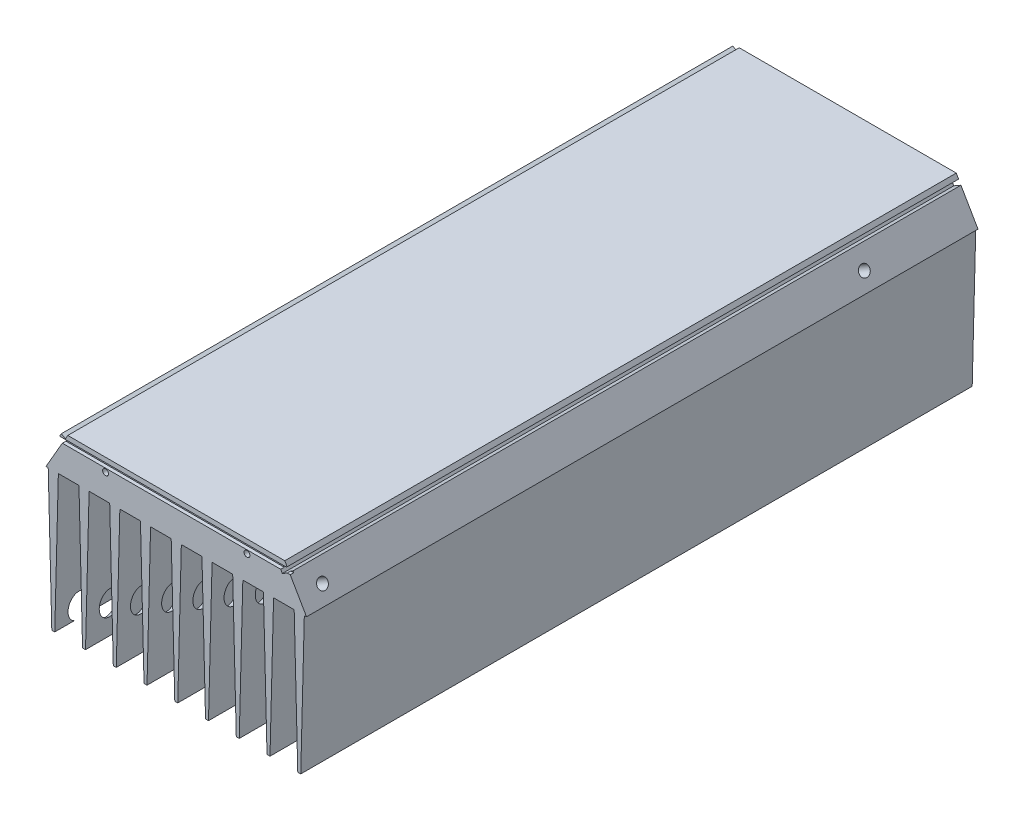
SolidWorks part; units mm, degrees
ref_plane "Plano frontal" through (0, 0, 0) normal (0, 0, 1) x (1, 0, 0)
ref_plane "Plano superior" through (0, 0, 0) normal (0, 1, 0) x (1, 0, 0)
ref_plane "Plano direito" through (0, 0, 0) normal (1, 0, 0) x (0, 0, -1)
sketch "Esboço1" plane through (0, 0, 0) normal (0, 0, 1) x (1, 0, 0)
  line L0 (0, 75) -> (135.77, 75)
  line L1 (135.77, 75) -> (135.77, 0)
  line L2 (0, 75) -> (0, 0)
  line L3 (0, 0) -> (135.77, 0) construction
  line L4 (0, 59) -> (4.785, 59) construction
  line L46 (4.785, 59) -> (13.535, 59)
  line L47 (13.535, 59) -> (17.835, 59) construction
  line L48 (17.835, 59) -> (26.585, 59)
  line L49 (26.585, 59) -> (30.885, 59) construction
  line L50 (30.885, 59) -> (39.635, 59)
  line L51 (39.635, 59) -> (43.935, 59) construction
  line L52 (43.935, 59) -> (52.685, 59)
  line L53 (52.685, 59) -> (56.985, 59) construction
  line L54 (56.985, 59) -> (65.735, 59)
  line L55 (65.735, 59) -> (70.035, 59) construction
  line L56 (70.035, 59) -> (78.785, 59)
  line L57 (78.785, 59) -> (83.085, 59) construction
  line L58 (83.085, 59) -> (91.835, 59)
  line L59 (91.835, 59) -> (96.135, 59) construction
  line L60 (96.135, 59) -> (104.885, 59)
  line L61 (104.885, 59) -> (109.185, 59) construction
  line L62 (109.185, 59) -> (117.935, 59)
  line L63 (117.935, 59) -> (122.235, 59) construction
  line L64 (122.235, 59) -> (130.985, 59)
  line L65 (130.985, 59) -> (135.77, 59) construction
  line L66 (4.785, 59) -> (3.2658, 0)
  line L67 (3.2658, 0) -> (0, 0)
  line L68 (13.535, 59) -> (15.0542, 0)
  line L69 (15.0542, 0) -> (16.3158, 0)
  line L70 (16.3158, 0) -> (17.835, 59)
  line L71 (26.585, 59) -> (28.1042, 0)
  line L72 (28.1042, 0) -> (29.3658, 0)
  line L73 (29.3658, 0) -> (30.885, 59)
  line L74 (39.635, 59) -> (41.1542, 0)
  line L75 (41.1542, 0) -> (42.4158, 0)
  line L76 (42.4158, 0) -> (43.935, 59)
  line L77 (52.685, 59) -> (54.2042, 0)
  line L78 (54.2042, 0) -> (55.4658, 0)
  line L79 (55.4658, 0) -> (56.985, 59)
  line L80 (65.735, 59) -> (67.2542, 0)
  line L81 (67.2542, 0) -> (68.5158, 0)
  line L82 (68.5158, 0) -> (70.035, 59)
  line L83 (78.785, 59) -> (80.3042, 0)
  line L84 (80.3042, 0) -> (81.5658, 0)
  line L85 (81.5658, 0) -> (83.085, 59)
  line L86 (91.835, 59) -> (93.3542, 0)
  line L87 (93.3542, 0) -> (94.6158, 0)
  line L88 (94.6158, 0) -> (96.135, 59)
  line L89 (104.885, 59) -> (106.4042, 0)
  line L90 (106.4042, 0) -> (107.6658, 0)
  line L91 (107.6658, 0) -> (109.185, 59)
  line L92 (117.935, 59) -> (119.4542, 0)
  line L93 (119.4542, 0) -> (120.7158, 0)
  line L94 (120.7158, 0) -> (122.235, 59)
  line L95 (130.985, 59) -> (132.5042, 0)
  line L96 (132.5042, 0) -> (135.77, 0)
  line L97 (67.885, 59) -> (67.885, 75) construction
  line L98 (15.685, 0) -> (15.685, 59) construction
  dimension "D1" = 135.77
  dimension "D2" = 75
  dimension "D3" = 8.75
  dimension "D4" = 4.3
  dimension "D5" = 16
  dimension "D6" = 2.95
extrude "Ressalto-extrusão1" add sketch "Esboço1" along normal blind 285
sketch "Esboço2" plane through (0, 0, 0) normal (0, 0, -1) x (-1, 0, 0)
  line L0 (-21.8312, 75) -> (-20.8312, 73.2679)
  line L1 (-135.77, 75) -> (0, 75) construction
  line L3 (-20.8312, 73.2679) -> (-19.0991, 74.2679)
  line L4 (-19.0991, 74.2679) -> (-18.0991, 72.5359)
  line L5 (-18.0991, 72.5359) -> (-19.8312, 71.5359)
  line L6 (-19.8312, 71.5359) -> (-12.5935, 59)
  line L7 (-4.785, 59) -> (-13.535, 59) construction
  line L8 (-12.5935, 59) -> (-12.5935, -2.8745)
  line L9 (-12.5935, -2.8745) -> (9.5022, -2.8745)
  line L10 (9.5022, -2.8745) -> (9.5022, 75)
  line L11 (9.5022, 75) -> (-21.8312, 75)
  line L12 (-113.9388, 75) -> (-114.9388, 73.2679)
  line L14 (-114.9388, 73.2679) -> (-111.9078, 71.5179)
  line L15 (-111.9078, 71.5179) -> (-112.9078, 69.7859)
  line L16 (-112.9078, 69.7859) -> (-115.9388, 71.5359)
  line L17 (-115.9388, 71.5359) -> (-123.1765, 59)
  line L18 (-122.235, 59) -> (-130.985, 59) construction
  line L19 (-123.1765, 59) -> (-123.1765, -2.8745)
  line L20 (-123.1765, -2.8745) -> (-142.2073, -2.8745)
  line L21 (-142.2073, -2.8745) -> (-142.2073, 78.515)
  line L22 (-142.2073, 78.515) -> (-113.9388, 78.515)
  line L23 (-113.9388, 78.515) -> (-113.9388, 75)
  line L25 (-113.9388, 75) -> (-21.8312, 75) construction
  line L26 (-67.885, 0) -> (-67.885, 75) construction
  line L27 (-67.2542, 0) -> (-68.5158, 0) construction
  dimension "D1" = 60
  dimension "D2" = 2
  dimension "D3" = 2
  dimension "D4" = 3.5
  dimension "D5" = 2
  dimension "D6" = 2
  dimension "D7" = 2
  dimension "D8" = 60
  dimension "D9" = 92.1077
extrude "Corte-extrusão1" cut sketch "Esboço2" against normal through all both and the other way through all
sketch "Esboço3" plane through (117.9301, 68.087, 0) normal (0.866, 0.5, 0) x (0, 0, -1)
  line L0 (-45, -4.0175) -> (-275, -4.0175) construction
  line L2 (-285, 3.9825) -> (0, 3.9825) construction
  line L3 (-285, -10.4927) -> (-285, 3.9825) construction
  circle A0 centre (-275, -4.0175) radius 2.25
  circle A1 centre (-45, -4.0175) radius 2.25
  dimension "D2" = 8
  dimension "D3" = 10
  dimension "D4" = 4.5
  dimension "D1" = 230
extrude "Corte-extrusão2" cut sketch "Esboço3" against normal blind 130
sketch "Esboço4" plane through (-16.1026, 9.2968, 0) normal (-0.866, 0.5, 0) x (0, 0, 1)
  line L0 (275, 63.8675) -> (45, 63.8675) construction
  line L1 (285, 71.8675) -> (285, 57.3923) construction
  line L2 (285, 71.8675) -> (0, 71.8675) construction
  circle A0 centre (45, 63.8675) radius 1.6455
  circle A1 centre (275, 63.8675) radius 1.6455
  dimension "D2" = 10
  dimension "D3" = 8
  dimension "D4" = 3.291
  dimension "D1" = 230
extrude "Corte-extrusão3" cut sketch "Esboço4" against normal blind 15
sketch "Esboço5" plane through (0, 0, 0) normal (0, 0, -1) x (-1, 0, 0)
  line L0 (-113.9388, 75) -> (-21.8312, 75) construction
  line L1 (-67.885, 75) -> (-67.885, 0) construction
  line L2 (-67.2542, 0) -> (-68.5158, 0) construction
  circle A0 centre (-67.885, 49.7676) radius 3.5
  dimension "D1" = 7
  dimension "D2" = 25.2324
extrude "Corte-extrusão4" cut sketch "Esboço5" against normal blind 10
sketch "Esboço6" plane through (117.9301, 68.087, 0) normal (0.866, 0.5, 0) x (0, 0, -1)
  circle A0 centre (-275, -4.0175) radius 4.5
  circle A1 centre (-45, -4.0175) radius 4.5
  dimension "D1" = 9
extrude "Corte-extrusão5" cut sketch "Esboço6" against normal blind 120 from offset 10 offset against normal yes
sketch "Esboço7" plane through (0, 36.4877, 0) normal (1, 0, 0) x (0, 0, -1)
  line L0 (-283.5, 36.5123) -> (-285, 36.5123)
  line L3 (-285, 36.5123) -> (-285, 34.5123)
  line L4 (-285, 34.5123) -> (-283.5, 34.5123)
  line L5 (-283.5, 34.5123) -> (-283.5, 36.5123)
  line L6 (-285, 35.0482) -> (-285, 22.5123) construction
  line L7 (-285, 34.5123) -> (-283.5, 34.5123) construction
  point P3 (-283.5, 36.5123)
  point P4 (-283.5, 34.5123)
  point P5 (-285, 34.5123)
  point P7 (-285, 5.5449)
  point P10 (-285, 5.6651)
  point P11 (-283.5, 34.5123)
extrude "Corte-extrusão6" cut sketch "Esboço7" against normal through all both and the other way through all
sketch "Esboço8" plane through (0, 0, 285) normal (0, 0, 1) x (1, 0, 0)
  circle A0 centre (37.885, 69.5) radius 1.25
  circle A1 centre (97.885, 69.5) radius 1.25
extrude "Corte-extrusão7" cut sketch "Esboço8" against normal blind 10
